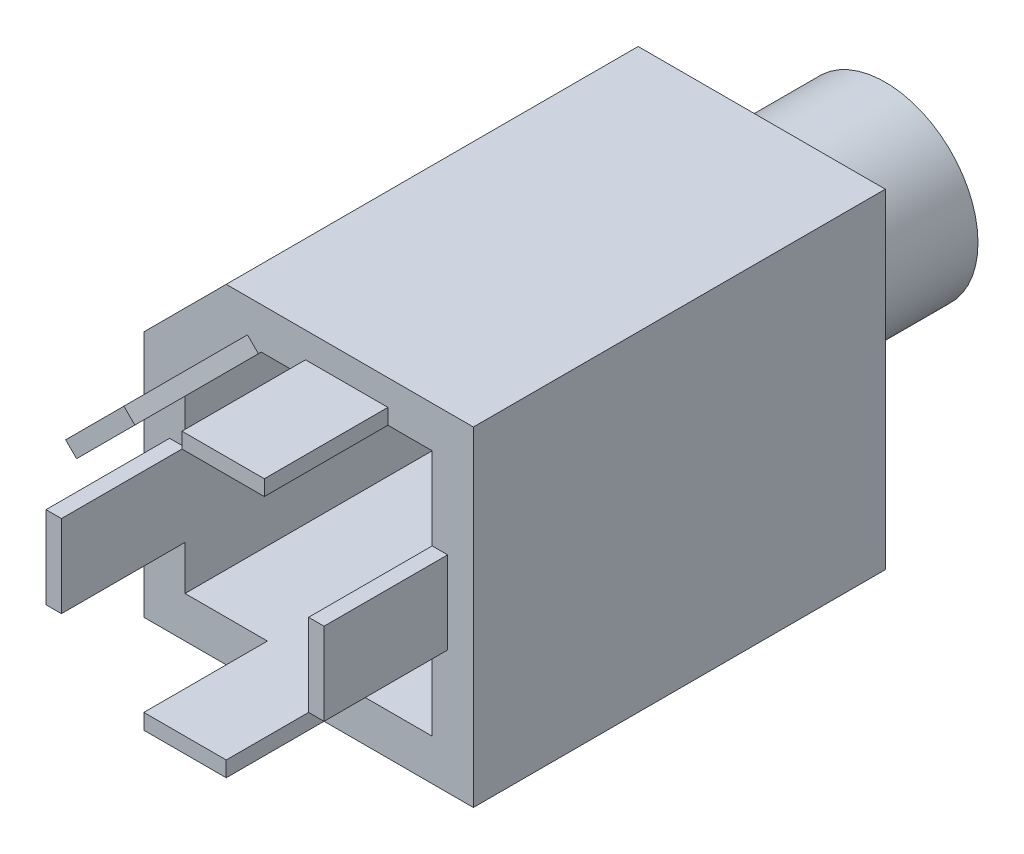
SolidWorks part; units mm, degrees
ref_plane "Plan de face" through (0, 0, 0) normal (0, 0, 1) x (1, 0, 0)
ref_plane "Plan de dessus" through (0, 0, 0) normal (0, 1, 0) x (1, 0, 0)
ref_plane "Plan de droite" through (0, 0, 0) normal (1, 0, 0) x (0, 0, -1)
sketch "Esquisse1" plane through (0, 0, 0) normal (0, 0, 1) x (1, 0, 0)
  line L0 (0, 0) -> (-16, 0)
  line L1 (-16, 0) -> (-16, 12)
  line L2 (-16, 12) -> (-12, 16)
  line L3 (-12, 16) -> (0, 16)
  line L4 (0, 16) -> (0, 0)
  circle A0 centre (-8, 8) radius 3.25
  dimension "D5" = 6.5
  dimension "D1" = 16
  dimension "D2" = 16
  dimension "D3" = 12
  dimension "D4" = 12
  dimension "D6" = 8
  dimension "D7" = 8
extrude "Boss.-Extru.1" add sketch "Esquisse1" along normal blind 2
sketch "Esquisse2" plane through (0, 0, 2) normal (0, 0, 1) x (1, 0, 0)
  line L0 (-16, 0) -> (0, 0)
  line L1 (0, 0) -> (0, 16)
  line L2 (0, 16) -> (-12, 16)
  line L3 (-12, 16) -> (-16, 12)
  line L4 (-16, 12) -> (-16, 0)
  line L5 (-2, 2) -> (-2, 14)
  line L6 (-2, 14) -> (-10.2994, 14)
  line L7 (-10.2994, 14) -> (-14, 10.2994)
  line L8 (-14, 10.2994) -> (-14, 2)
  line L9 (-14, 2) -> (-2, 2)
  dimension "D1" = 2
  dimension "D2" = 2
  dimension "D3" = 2
  dimension "D4" = 2
extrude "Boss.-Extru.2" add sketch "Esquisse2" along normal blind 18
sketch "Esquisse3" plane through (0, 0, 0) normal (0, 0, -1) x (-1, 0, 0)
  circle A0 centre (8, 8) radius 4.5
  circle A1 centre (8, 8) radius 3.25
  dimension "D1" = 9
  dimension "D2" = 6.5
extrude "Boss.-Extru.3" add sketch "Esquisse3" along normal blind 8
sketch "Esquisse4" plane through (0, 0, 0) normal (0, 0, -1) x (-1, 0, 0)
  line L2 (2.5, 5.3284) -> (2.5, 10.6716)
  line L4 (5.3284, 13.5) -> (10.6716, 13.5)
  line L7 (13.5, 10.6716) -> (13.5, 5.3284)
  line L9 (10.6716, 2.5) -> (5.3284, 2.5)
  line L10 (16, 12) -> (16, 0) construction
  line L11 (16, 0) -> (0, 0) construction
  line L12 (2.5, 10.6716) -> (2.8536, 10.318)
  line L13 (2.8536, 10.318) -> (5.682, 13.1464)
  line L14 (5.682, 13.1464) -> (5.3284, 13.5)
  line L15 (2.5, 5.3284) -> (2.8536, 5.682)
  line L16 (2.8536, 5.682) -> (5.682, 2.8536)
  line L17 (5.682, 2.8536) -> (5.3284, 2.5)
  line L18 (10.6716, 2.5) -> (10.318, 2.8536)
  line L19 (10.318, 2.8536) -> (13.1464, 5.682)
  line L20 (13.1464, 5.682) -> (13.5, 5.3284)
  line L21 (13.5, 10.6716) -> (13.1464, 10.318)
  line L22 (13.1464, 10.318) -> (10.318, 13.1464)
  line L23 (10.318, 13.1464) -> (10.6716, 13.5)
  circle A0 centre (8, 8) radius 3.25
  dimension "D6" = 6.5
  dimension "D1" = 11
  dimension "D2" = 11
  dimension "D3" = 2.5
  dimension "D4" = 2.5
  dimension "D5" = 4
  dimension "D7" = 0.5
extrude "Boss.-Extru.4" add sketch "Esquisse4" along normal blind 1
sketch "Esquisse11" plane through (-3.7322, -3.7322, 0) normal (-0.7071, -0.7071, 0) x (0, 0, 1)
  line L0 (0, 9.3137) -> (-1, 9.3137)
  line L1 (-1, 9.3137) -> (-2.3266, 11.3137)
  line L2 (-2.3266, 11.3137) -> (-1, 13.3137)
  line L3 (-1, 13.3137) -> (0, 13.3137)
  line L4 (0, 13.3137) -> (0, 9.3137)
  dimension "D1" = 2.4
extrude "Boss.-Extru.6" add sketch "Esquisse11" along normal blind 0.5
sketch "Esquisse12" plane through (-4.2678, 4.2678, 0) normal (0.7071, -0.7071, 0) x (0, 0, -1)
  line L0 (0, 2) -> (1, 2)
  line L1 (1, 2) -> (2.3266, 0)
  line L2 (2.3266, 0) -> (1, -2)
  line L3 (1, -2) -> (0, -2)
  line L4 (0, -2) -> (0, 2)
  dimension "D1" = 2.4
extrude "Boss.-Extru.7" add sketch "Esquisse12" along normal blind 0.5
sketch "Esquisse13" plane through (3.7322, 3.7322, 0) normal (0.7071, 0.7071, 0) x (0, 0, -1)
  line L0 (0, 13.3137) -> (1, 13.3137)
  line L1 (1, 13.3137) -> (2.3266, 11.3137)
  line L2 (2.3266, 11.3137) -> (1, 9.3137)
  line L3 (1, 9.3137) -> (0, 9.3137)
  line L4 (0, 9.3137) -> (0, 13.3137)
  dimension "D1" = 2.4
extrude "Boss.-Extru.8" add sketch "Esquisse13" along normal blind 0.5
sketch "Esquisse14" plane through (-11.7322, 11.7322, 0) normal (-0.7071, 0.7071, 0) x (0, 0, 1)
  line L0 (0, -2) -> (-1, -2)
  line L1 (-1, -2) -> (0, -2) construction
  line L2 (-1, -2) -> (-2.3266, 0)
  line L3 (-2.3266, 0) -> (-1, 2)
  line L4 (-1, 2) -> (0, 2)
  line L5 (0, 2) -> (0, -2)
  dimension "D1" = 2.4
extrude "Boss.-Extru.9" add sketch "Esquisse14" along normal blind 0.5
sketch "Esquisse15" plane through (0, 0, 20) normal (0, 0, 1) x (1, 0, 0)
  line L0 (-14, 10.2994) -> (-14, 2) construction
  line L1 (-14, 4.15) -> (-14.75, 4.15)
  line L2 (-14, 4.15) -> (-14, 8.15)
  line L3 (-14, 8.15) -> (-14.75, 8.15)
  line L4 (-14.75, 4.15) -> (-14.75, 8.15)
  line L5 (-14, 2) -> (-2, 2) construction
  line L6 (-6, 2) -> (-10, 2)
  line L7 (-6, 2) -> (-6, 1.25)
  line L8 (-6, 1.25) -> (-10, 1.25)
  line L9 (-10, 2) -> (-10, 1.25)
  line L10 (-2, 2) -> (-2, 14) construction
  line L11 (-2, 6) -> (-1.25, 6)
  line L12 (-2, 6) -> (-2, 10)
  line L13 (-2, 10) -> (-1.25, 10)
  line L14 (-1.25, 6) -> (-1.25, 10)
  line L15 (-2, 14) -> (-10.2994, 14) construction
  line L16 (-4.15, 14) -> (-8.15, 14)
  line L17 (-4.15, 14) -> (-4.15, 14.75)
  line L18 (-4.15, 14.75) -> (-8.15, 14.75)
  line L19 (-8.15, 14) -> (-8.15, 14.75)
  line L20 (-10.4372, 13.8622) -> (-13.2656, 11.0337)
  line L21 (-10.4372, 13.8622) -> (-10.9676, 14.3925)
  line L22 (-13.2656, 11.0337) -> (-13.796, 11.5641)
  line L23 (-10.9676, 14.3925) -> (-13.796, 11.5641)
  line L24 (-10.2994, 14) -> (-14, 10.2994) construction
  dimension "D1" = 4
  dimension "D2" = 4
  dimension "D3" = 4
  dimension "D4" = 4
  dimension "D5" = 4
  dimension "D6" = 0.75
  dimension "D7" = 4
  dimension "D8" = 4
  dimension "D9" = 2.15
  dimension "D10" = 2.15
extrude "Boss.-Extru.10" add sketch "Esquisse15" along normal blind 6
